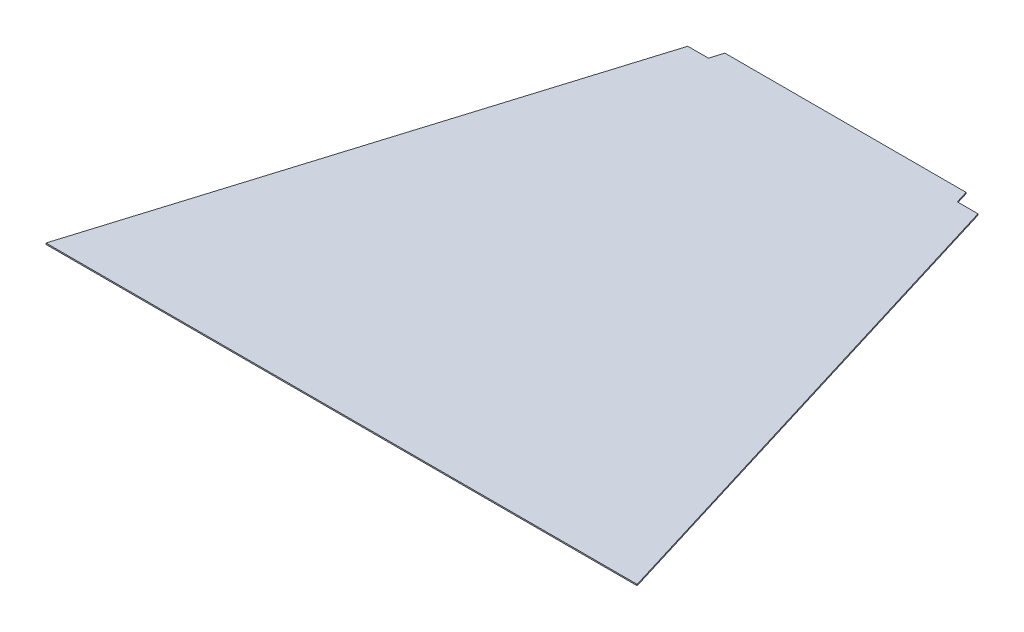
SolidWorks part; units mm, degrees
material "6061 Alloy"
ref_plane "Front Plane" through (0, 0, 0) normal (0, 0, 1) x (1, 0, 0)
ref_plane "Top Plane" through (0, 0, 0) normal (0, 1, 0) x (1, 0, 0)
ref_plane "Right Plane" through (0, 0, 0) normal (1, 0, 0) x (0, 0, -1)
sketch "Sketch1" plane through (0, 0, 0) normal (0, 1, 0) x (1, 0, 0)
  line L1 (-4.5843, 0) -> (-4.5843, -635) construction
  line L2 (-186.4008, 16.1336) -> (-374.9163, -599.4016)
  line L3 (177.2323, 16.1336) -> (365.7477, -599.4016)
  line L4 (-374.9163, -599.4016) -> (365.7477, -599.4016)
  line L6 (-186.4008, 16.1336) -> (-160.4928, 16.1336)
  line L7 (151.3243, 16.1336) -> (177.2323, 16.1336)
  line L8 (-160.4928, 16.1336) -> (-155.6581, 31.9199)
  line L9 (151.3243, 16.1336) -> (146.4895, 31.9199)
  line L10 (-155.6581, 31.9199) -> (146.4895, 31.9199)
  point P4 (0, 0)
  point P12 (-4.5843, 0)
  dimension "D1" = 72.972
  dimension "D2" = 740.664
  dimension "D3" = 643.756
extrude "Boss-Extrude1" add sketch "Sketch1" along normal blind 1.5875
sketch "Sketch2" plane through (0, 0, 0) normal (0, -1, 0) x (1, 0, 0)
  line L0 (-4.5843, -31.9199) -> (-4.5843, 599.4016) construction
  line L1 (146.4895, -31.9199) -> (-155.6581, -31.9199) construction
  line L2 (-374.9163, 599.4016) -> (365.7477, 599.4016) construction
sketch "Sketch3" plane through (0, 0, 599.4016) normal (0, 0, 1) x (1, 0, 0)
  line L0 (-4.5843, 0) -> (-4.5843, 14.2875) construction
  line L1 (-374.9163, 0) -> (365.7477, 0) construction
  dimension "D1" = 14.2875
